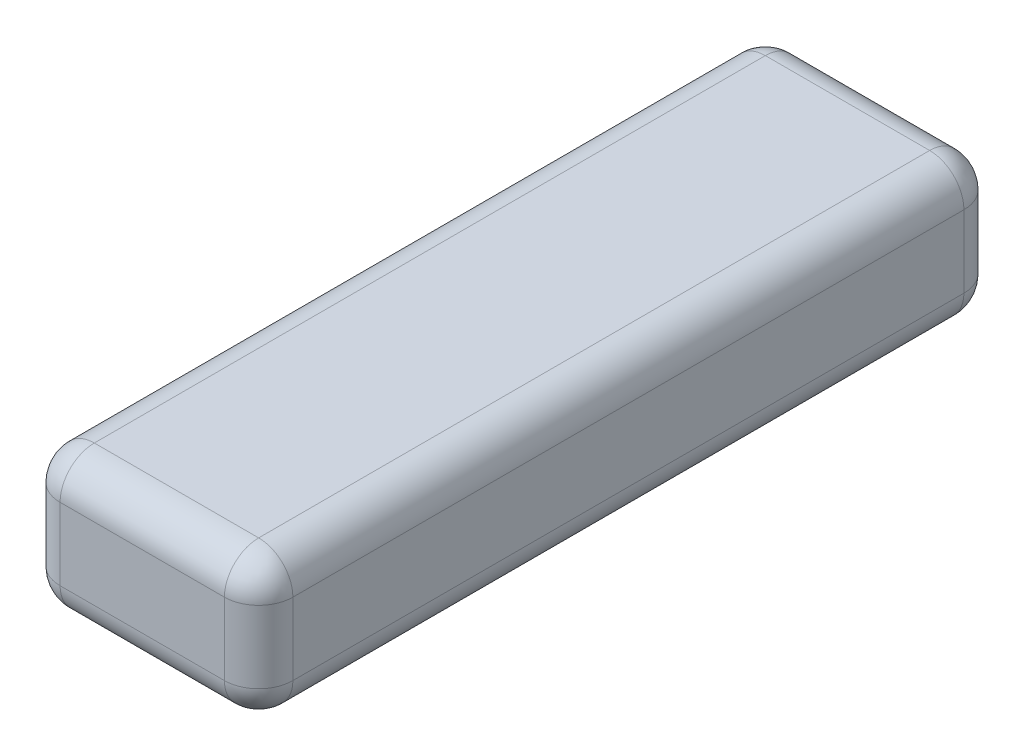
SolidWorks part; units mm, degrees
ref_plane "Plan de face" through (0, 0, 0) normal (0, 0, 1) x (1, 0, 0)
ref_plane "Plan de dessus" through (0, 0, 0) normal (0, 1, 0) x (1, 0, 0)
ref_plane "Plan de droite" through (0, 0, 0) normal (1, 0, 0) x (0, 0, -1)
sketch "Esquisse1" plane through (0, 0, 0) normal (0, 1, 0) x (1, 0, 0)
  line L1 (-17, -54) -> (17, -54)
  line L2 (-17, -54) -> (-17, 54)
  line L3 (-17, 54) -> (17, 54)
  line L4 (17, -54) -> (17, 54)
  line L5 (-17, -54) -> (17, 54) construction
  line L6 (-17, 54) -> (17, -54) construction
  point P0 (0, 0)
  dimension "D1" = 108
  dimension "D2" = 34
extrude "Boss.-Extru.1" add sketch "Esquisse1" along normal blind 10.5 and the other way blind 10.05
fillet "Congé1" radius 5 4 edges at (17, 0.225, -54) (-17, 0.225, -54) (-17, 0.225, 54) (17, 0.225, 54)
fillet "Congé2" radius 5 16 edges at (17, -10.05, 0) (15.5355, -10.05, -52.5355) (0, -10.05, -54) (-15.5355, -10.05, -52.5355) (-17, -10.05, 0) (-15.5355, -10.05, 52.5355) (0, -10.05, 54) (0, 10.5, 54) (-15.5355, 10.5, 52.5355) (-17, 10.5, 0) (-15.5355, 10.5, -52.5355) (0, 10.5, -54) (15.5355, 10.5, -52.5355) (17, 10.5, 0) (15.5355, -10.05, 52.5355) (15.5355, 10.5, 52.5355)
